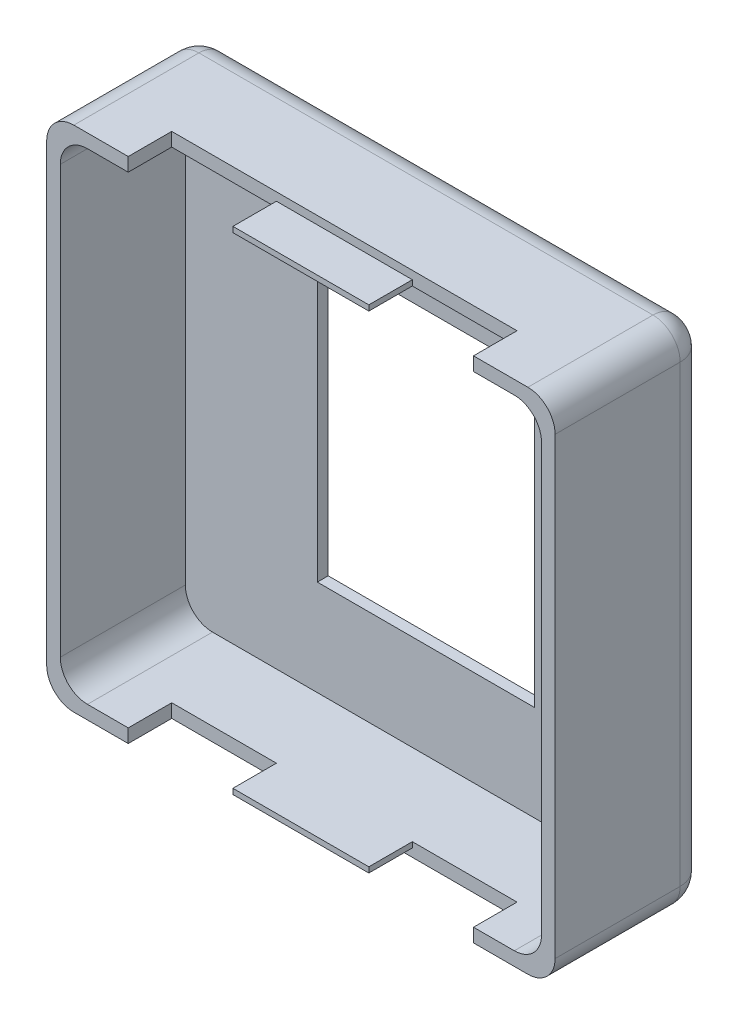
SolidWorks part; units mm, degrees
ref_plane "Front Plane" through (0, 0, 0) normal (0, 0, 1) x (1, 0, 0)
ref_plane "Top Plane" through (0, 0, 0) normal (0, 1, 0) x (1, 0, 0)
ref_plane "Right Plane" through (0, 0, 0) normal (1, 0, 0) x (0, 0, -1)
sketch "Sketch1" plane through (0, 0, 0) normal (0, 0, 1) x (1, 0, 0)
  line L1 (-21.209, -23.749) -> (21.209, -23.749)
  line L2 (-23.749, -21.209) -> (-23.749, 21.209)
  line L3 (-21.209, 23.749) -> (21.209, 23.749)
  line L4 (23.749, -21.209) -> (23.749, 21.209)
  line L5 (-23.749, -23.749) -> (23.749, 23.749) construction
  line L6 (-23.749, 23.749) -> (23.749, -23.749) construction
  arc A0 (-21.209, -23.749) -> (-23.749, -21.209) centre (-21.209, -21.209) cw
  arc A1 (21.209, -23.749) -> (23.749, -21.209) centre (21.209, -21.209) ccw
  arc A2 (21.209, 23.749) -> (23.749, 21.209) centre (21.209, 21.209) cw
  arc A3 (-23.749, 21.209) -> (-21.209, 23.749) centre (-21.209, 21.209) cw
  point P0 (0, 0)
  dimension "D3" = 2.54
  dimension "D1" = 47.498
  dimension "D2" = 47.498
extrude "Boss-Extrude1" add sketch "Sketch1" along normal blind 14.224
sketch "Sketch2" plane through (0, 0, 14.224) normal (0, 0, 1) x (1, 0, 0)
  line L22 (21.209, 23.749) -> (-21.209, 23.749) construction
  line L23 (19.939, -22.479) -> (-19.939, -22.479)
  line L24 (22.479, -19.939) -> (22.479, 19.939)
  line L25 (19.939, 22.479) -> (-19.939, 22.479)
  line L26 (-22.479, -19.939) -> (-22.479, 19.939)
  line L27 (22.479, -22.479) -> (-22.479, 22.479) construction
  line L28 (22.479, 22.479) -> (-22.479, -22.479) construction
  line L29 (-23.749, 21.209) -> (-23.749, -21.209) construction
  arc A14 (-19.939, -22.479) -> (-22.479, -19.939) centre (-19.939, -19.939) cw
  arc A15 (19.939, -22.479) -> (22.479, -19.939) centre (19.939, -19.939) ccw
  arc A16 (22.479, 19.939) -> (19.939, 22.479) centre (19.939, 19.939) ccw
  arc A17 (-19.939, 22.479) -> (-22.479, 19.939) centre (-19.939, 19.939) ccw
  point P12 (0, 0)
  dimension "D3" = 2.54
  dimension "D1" = 1.27
  dimension "D2" = 1.27
extrude "Cut-Extrude1" cut sketch "Sketch2" against normal blind 11.684
fillet "Fillet1" radius 2.54 8 edges at (-23.0051, 23.0051, 0) (0, 23.749, 0) (23.0051, 23.0051, 0) (23.749, 0, 0) (23.0051, -23.0051, 0) (0, -23.749, 0) (-23.0051, -23.0051, 0) (-23.749, 0, 0)
sketch "Sketch3" plane through (0, 23.749, 0) normal (0, 1, 0) x (1, 0, 0)
  line L0 (21.209, -14.224) -> (-21.209, -14.224) construction
  line L1 (16.129, -18.288) -> (-16.129, -18.288)
  line L2 (16.129, -18.288) -> (16.129, -10.16)
  line L3 (16.129, -10.16) -> (-16.129, -10.16)
  line L4 (-16.129, -18.288) -> (-16.129, -10.16)
  line L5 (16.129, -18.288) -> (-16.129, -10.16) construction
  line L6 (16.129, -10.16) -> (-16.129, -18.288) construction
  point P0 (0, -14.224)
  dimension "D1" = 32.258
  dimension "D2" = 4.064
extrude "Cut-Extrude2" cut sketch "Sketch3" against normal through all both and the other way through all
sketch "Sketch4" plane through (23.749, 0, 0) normal (1, 0, 0) x (0, 0, -1)
  line L0 (-14.224, -21.209) -> (-14.224, 21.209) construction
  circle A0 centre (-14.224, -14.986) radius 1.778
  point P4 (-14.224, 0)
  dimension "D2" = 3.556
  dimension "D1" = 14.986
sketch "Sketch5" plane through (0, 0, 0) normal (0, 0, -1) x (-1, 0, 0)
  line L1 (-13.462, 17.145) -> (13.462, 17.145)
  line L2 (-13.462, 17.145) -> (-13.462, -17.145)
  line L3 (-13.462, -17.145) -> (13.462, -17.145)
  line L4 (13.462, 17.145) -> (13.462, -17.145)
  line L5 (-13.462, 17.145) -> (13.462, -17.145) construction
  line L6 (-13.462, -17.145) -> (13.462, 17.145) construction
  point P0 (0, 0)
  dimension "D1" = 26.924
  dimension "D2" = 34.29
extrude "Cut-Extrude4" cut sketch "Sketch5" against normal blind 1.524
sketch "Sketch6" plane through (0, 0, 1.524) normal (0, 0, -1) x (-1, 0, 0)
  line L1 (-10.1453, -13.5361) -> (10.1453, -13.5361)
  line L2 (-10.1453, -13.5361) -> (-10.1453, 13.5361)
  line L3 (-10.1453, 13.5361) -> (10.1453, 13.5361)
  line L4 (10.1453, -13.5361) -> (10.1453, 13.5361)
  line L5 (-10.1453, -13.5361) -> (10.1453, 13.5361) construction
  line L6 (-10.1453, 13.5361) -> (10.1453, -13.5361) construction
  point P0 (0, 0)
extrude "Cut-Extrude5" cut sketch "Sketch6" against normal blind 1.524
sketch "Sketch7" plane through (0, 0, 0) normal (0, 0, -1) x (-1, 0, 0)
  line L0 (21.209, 21.209) -> (21.209, -21.209) construction
  line L1 (21.209, 21.209) -> (-21.209, 21.209) construction
  line L2 (-21.209, -21.209) -> (21.209, -21.209) construction
  line L3 (13.589, 21.209) -> (13.589, -21.209) construction
  line L4 (21.209, -21.209) -> (21.209, 21.209) construction
  line L5 (13.589, 17.145) -> (21.209, 17.145) construction
  line L6 (19.939, 17.145) -> (21.209, 17.145)
  line L7 (14.859, 17.145) -> (13.589, 17.145)
  line L8 (21.209, 15.875) -> (16.129, 15.875)
  line L9 (21.209, 10.795) -> (16.129, 10.795)
  line L10 (16.129, 14.605) -> (21.209, 14.605)
  line L11 (21.209, 14.605) -> (21.209, 15.875)
  line L12 (16.129, 12.065) -> (21.209, 12.065)
  line L13 (21.209, 12.065) -> (21.209, 10.795)
  line L14 (13.589, 9.525) -> (21.209, 9.525)
  line L15 (21.209, 9.525) -> (21.209, 5.715)
  line L16 (21.209, 5.715) -> (19.939, 5.715)
  line L17 (19.939, 5.715) -> (19.939, 8.255)
  line L18 (19.939, 8.255) -> (18.034, 8.255)
  line L19 (18.034, 8.255) -> (18.034, 6.985)
  line L20 (18.034, 6.985) -> (16.764, 6.985)
  line L21 (16.764, 6.985) -> (16.764, 8.255)
  line L22 (16.764, 8.255) -> (13.589, 8.255)
  line L23 (13.589, 8.255) -> (13.589, 9.525)
  line L24 (13.589, 4.445) -> (21.209, 4.445)
  line L25 (21.209, 4.445) -> (21.209, 0.635)
  line L26 (21.209, 0.635) -> (19.939, 0.635)
  line L27 (19.939, 0.635) -> (19.939, 3.175)
  line L28 (19.939, 3.175) -> (18.034, 3.175)
  line L29 (18.034, 3.175) -> (18.034, 1.905)
  line L30 (18.034, 1.905) -> (16.764, 1.905)
  line L31 (16.764, 1.905) -> (16.764, 3.175)
  line L32 (16.764, 3.175) -> (13.589, 3.175)
  line L33 (13.589, 3.175) -> (13.589, 4.445)
  line L34 (21.209, -0.635) -> (13.589, -0.635)
  line L35 (13.589, -0.635) -> (13.589, -4.445)
  line L36 (13.589, -4.445) -> (14.859, -4.445)
  line L37 (14.859, -4.445) -> (14.859, -1.905)
  line L38 (14.859, -1.905) -> (21.209, -1.905)
  line L39 (21.209, -1.905) -> (21.209, -0.635)
  line L40 (13.589, -5.715) -> (21.209, -5.715)
  line L41 (21.209, -5.715) -> (21.209, -9.525)
  line L42 (21.209, -9.525) -> (19.939, -9.525)
  line L43 (19.939, -9.525) -> (19.939, -6.985)
  line L44 (19.939, -6.985) -> (18.034, -6.985)
  line L45 (18.034, -6.985) -> (18.034, -8.255)
  line L46 (18.034, -8.255) -> (16.764, -8.255)
  line L47 (16.764, -8.255) -> (16.764, -6.985)
  line L48 (16.764, -6.985) -> (14.859, -6.985)
  line L49 (14.859, -6.985) -> (14.859, -9.525)
  line L50 (14.859, -9.525) -> (13.589, -9.525)
  line L51 (13.589, -9.525) -> (13.589, -5.715)
  line L52 (13.589, -13.0175) -> (21.209, -13.0175) construction
  line L53 (21.209, -13.0175) -> (17.399, -13.0175) construction
  line L54 (17.399, -13.0175) -> (13.589, -13.0175) construction
  line L55 (18.9865, -13.97) -> (18.9865, -15.24)
  line L56 (15.8115, -12.065) -> (15.8115, -10.795)
  line L57 (13.589, -18.7325) -> (21.209, -18.7325) construction
  line L58 (15.8115, -17.78) -> (15.8115, -16.51)
  line L59 (18.9865, -20.955) -> (18.9865, -19.685)
  arc A0 (21.209, 17.145) -> (13.589, 17.145) centre (17.399, 17.145) ccw
  arc A1 (19.939, 17.145) -> (14.859, 17.145) centre (17.399, 17.145) ccw
  arc A2 (16.129, 15.875) -> (16.129, 10.795) centre (16.129, 13.335) ccw
  arc A3 (16.129, 14.605) -> (16.129, 12.065) centre (16.129, 13.335) ccw
  arc A4 (18.9865, -15.24) -> (16.764, -13.0175) centre (18.9865, -13.0175) ccw
  arc A5 (15.8115, -10.795) -> (18.034, -13.0175) centre (15.8115, -13.0175) ccw
  arc A6 (18.9865, -13.97) -> (18.034, -13.0175) centre (18.9865, -13.0175) ccw
  arc A7 (15.8115, -12.065) -> (16.764, -13.0175) centre (15.8115, -13.0175) ccw
  arc A8 (15.8115, -16.51) -> (18.034, -18.7325) centre (15.8115, -18.7325) ccw
  arc A9 (18.9865, -20.955) -> (16.764, -18.7325) centre (18.9865, -18.7325) ccw
  arc A10 (15.8115, -17.78) -> (16.764, -18.7325) centre (15.8115, -18.7325) ccw
  arc A11 (18.9865, -19.685) -> (18.034, -18.7325) centre (18.9865, -18.7325) ccw
  point P15 (13.589, 0)
  dimension "D3" = 5.08
  dimension "D4" = 17.145
  dimension "D5" = 2.54
  dimension "D6" = 5.08
  dimension "D40" = 4.445
  dimension "D41" = 1.27
  dimension "D42" = 1.905
  dimension "D43" = 4.445
  dimension "D44" = 1.27
  dimension "D46" = 1.905
  dimension "D1" = 7.62
  dimension "D2" = 0
  dimension "D7" = 1.27
  dimension "D8" = 1.27
  dimension "D9" = 1.27
  dimension "D10" = 1.27
  dimension "D11" = 1.27
  dimension "D12" = 1.27
  dimension "D13" = 1.905
  dimension "D14" = 1.27
  dimension "D15" = 2.54
  dimension "D16" = 3.81
  dimension "D17" = 1.27
  dimension "D18" = 1.27
  dimension "D19" = 1.27
  dimension "D20" = 1.27
  dimension "D21" = 1.905
  dimension "D22" = 1.27
  dimension "D23" = 2.54
  dimension "D24" = 3.81
  dimension "D25" = 1.27
  dimension "D26" = 1.27
  dimension "D27" = 1.27
  dimension "D28" = 3.81
  dimension "D29" = 1.27
  dimension "D30" = 1.27
  dimension "D31" = 1.27
  dimension "D32" = 1.27
  dimension "D33" = 1.27
  dimension "D34" = 2.54
  dimension "D35" = 2.54
  dimension "D36" = 3.81
  dimension "D37" = 3.81
  dimension "D38" = 1.905
  dimension "D39" = 1.27
extrude "Boss-Extrude2" add sketch "Sketch7" along normal blind 0.762
sketch "Sketch8" plane through (0, 0, 10.16) normal (0, 0, 1) x (1, 0, 0)
  line L0 (16.129, 22.479) -> (-16.129, 22.479) construction
  line L1 (6.35, 22.987) -> (-6.35, 22.987)
  line L2 (6.35, 22.987) -> (6.35, 22.479)
  line L3 (6.35, 22.479) -> (-6.35, 22.479)
  line L4 (-6.35, 22.987) -> (-6.35, 22.479)
  line L5 (6.35, 22.987) -> (-6.35, 22.479) construction
  line L6 (6.35, 22.479) -> (-6.35, 22.987) construction
  line L7 (-16.129, -22.479) -> (16.129, -22.479) construction
  line L8 (6.35, -22.987) -> (-6.35, -22.987)
  line L9 (6.35, -22.987) -> (6.35, -22.479)
  line L10 (6.35, -22.479) -> (-6.35, -22.479)
  line L11 (-6.35, -22.987) -> (-6.35, -22.479)
  line L12 (6.35, -22.987) -> (-6.35, -22.479) construction
  line L13 (6.35, -22.479) -> (-6.35, -22.987) construction
  point P0 (0, 22.733)
  point P7 (0, -22.733)
  dimension "D1" = 0.508
  dimension "D2" = 12.7
  dimension "D3" = 0
  dimension "D4" = 0.508
  dimension "D5" = 12.7
  dimension "D6" = 0
extrude "Boss-Extrude3" add sketch "Sketch8" along normal blind 4.064
